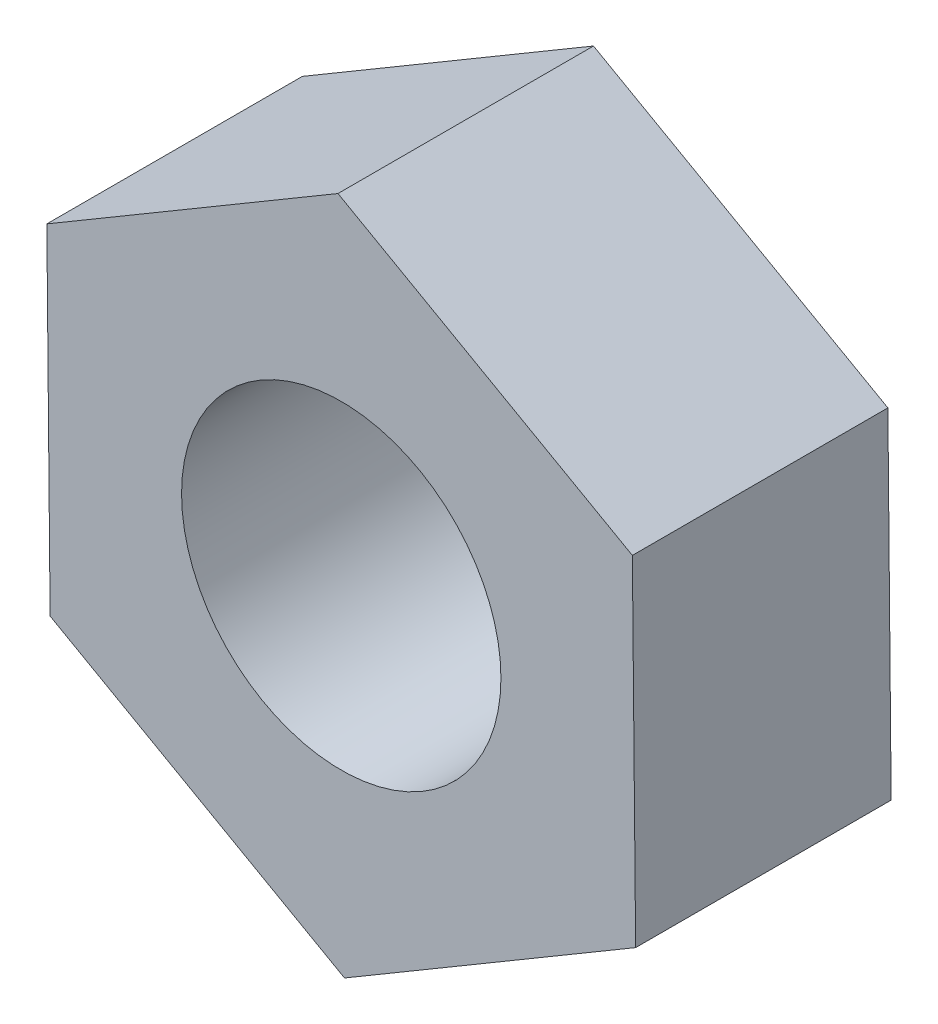
SolidWorks part; units mm, degrees
ref_plane "前视基准面" through (0, 0, 0) normal (0, 0, 1) x (1, 0, 0)
ref_plane "上视基准面" through (0, 0, 0) normal (0, 1, 0) x (1, 0, 0)
ref_plane "右视基准面" through (0, 0, 0) normal (1, 0, 0) x (0, 0, -1)
sketch "草图1" plane through (0, 0, 0) normal (0, 0, 1) x (1, 0, 0)
  line L1 (-3.6205, 22.5434) -> (-3.6512, 25.7186)
  line L2 (-3.6512, 25.7186) -> (-6.4165, 27.2797)
  line L3 (-6.4165, 27.2797) -> (-9.151, 25.6654)
  line L4 (-9.151, 25.6654) -> (-9.1202, 22.4901)
  line L5 (-9.1202, 22.4901) -> (-6.355, 20.9291)
  line L6 (-6.355, 20.9291) -> (-3.6205, 22.5434)
  circle A0 centre (-6.3857, 24.1044) radius 2.75 construction
  circle A1 centre (-6.3857, 24.1044) radius 1.5
extrude "凸台-拉伸1" add sketch "草图1" along normal blind 2.4
